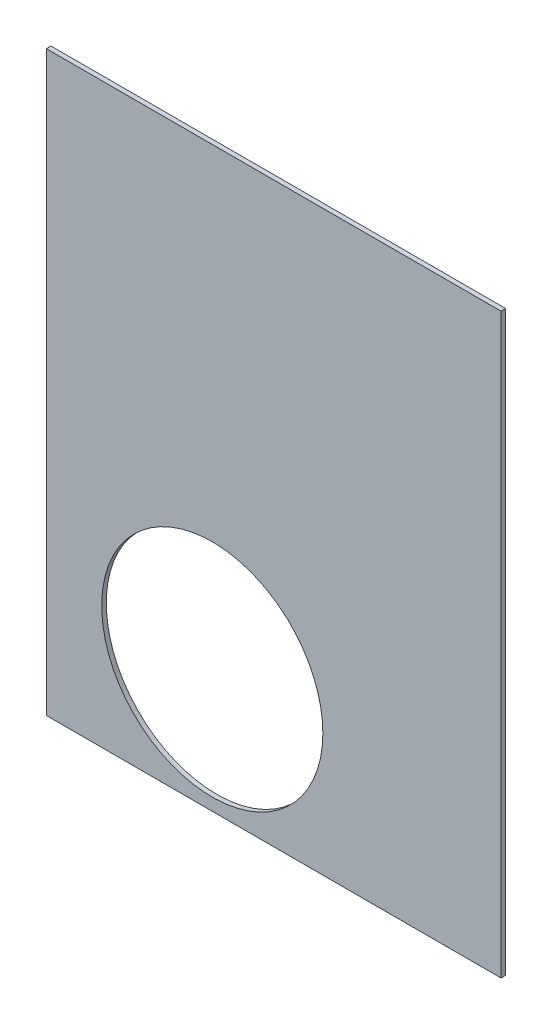
SolidWorks part; units mm, degrees
ref_plane "Front Plane" through (0, 0, 0) normal (0, 0, 1) x (1, 0, 0)
ref_plane "Top Plane" through (0, 0, 0) normal (0, 1, 0) x (1, 0, 0)
ref_plane "Right Plane" through (0, 0, 0) normal (1, 0, 0) x (0, 0, -1)
sketch "Sketch1" plane through (0, 0, 0) normal (0, 0, 1) x (1, 0, 0)
  line L0 (-35, 7.5) -> (-35, 97.5) construction
  line L1 (-35, 97.5) -> (35, 97.5) construction
  line L2 (35, 97.5) -> (35, 7.5) construction
  line L3 (35, 7.5) -> (-35, 7.5) construction
  line L4 (-35, 7.5) -> (-35, 97.5) construction
  line L5 (-35, 97.5) -> (35, 97.5) construction
  line L6 (35, 97.5) -> (35, 7.5) construction
  line L7 (35, 7.5) -> (-35, 7.5) construction
  line L8 (-37, 5.5) -> (-37, 99.5)
  line L9 (-37, 99.5) -> (37, 99.5)
  line L10 (37, 99.5) -> (37, 5.5)
  line L11 (37, 5.5) -> (-37, 5.5)
  dimension "D1" = 2
extrude "Boss-Extrude1" add sketch "Sketch1" along normal blind 0.75
sketch "Sketch3" plane through (0, 0, 0.75) normal (0, 0, 1) x (1, 0, 0)
  circle A1 centre (-10, 25.5) radius 18 construction
  circle A2 centre (-10, 25.5) radius 18.5 construction
  circle A3 centre (-10, 25.5) radius 18
  dimension "D1" = 0.5
extrude "Cut-Extrude1" cut sketch "Sketch3" against normal through all
